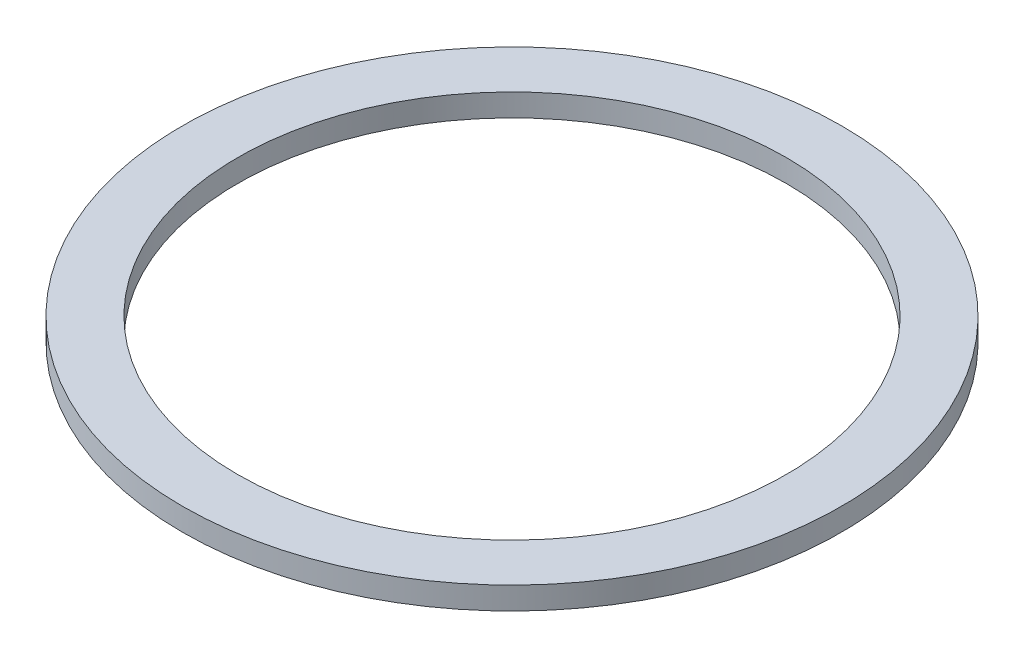
SolidWorks part; units mm, degrees
ref_plane "Front Plane" through (0, 0, 0) normal (0, 0, 1) x (1, 0, 0)
ref_plane "Top Plane" through (0, 0, 0) normal (0, 1, 0) x (1, 0, 0)
ref_plane "Right Plane" through (0, 0, 0) normal (1, 0, 0) x (0, 0, -1)
sketch "Sketch1" plane through (0, 0, 0) normal (0, 1, 0) x (1, 0, 0)
  circle A0 centre (0, 0) radius 12.2
  circle A1 centre (0, 0) radius 14.65
  dimension "D1" = 29.3
  dimension "D2" = 24.4
extrude "Boss-Extrude1" add sketch "Sketch1" along normal blind 1
